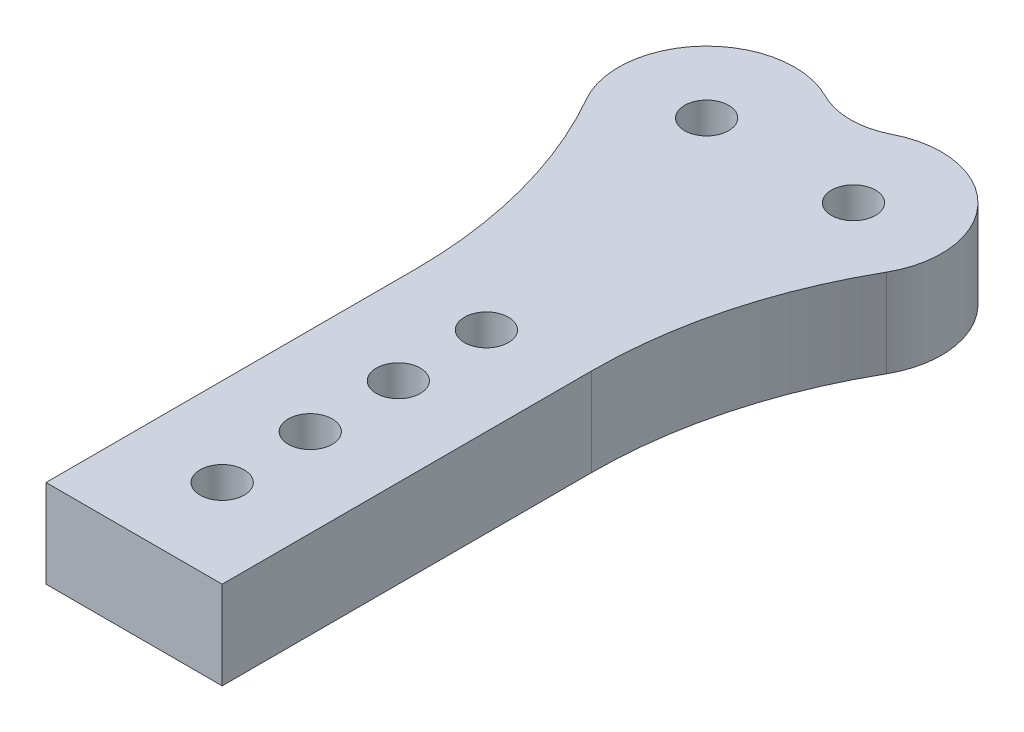
SolidWorks part; units mm, degrees
ref_plane "Alzado" through (0, 0, 0) normal (0, 0, 1) x (1, 0, 0)
ref_plane "Planta" through (0, 0, 0) normal (0, 1, 0) x (1, 0, 0)
ref_plane "Vista lateral" through (0, 0, 0) normal (1, 0, 0) x (0, 0, -1)
sketch "Croquis2" plane through (0, 0, 0) normal (0, 1, 0) x (1, 0, 0)
  line L5 (-14.213, -7.8357) -> (-14.2804, -16.8354) construction
  line L6 (-16.9314, -1.1122) -> (-10.9314, -1.1122) construction
  line L9 (-16.9314, -23.1122) -> (-10.9314, -23.1122)
  line L11 (-16.9314, -1.1122) -> (-10.9314, -1.1122)
  line L13 (-16.9314, -1.1122) -> (-16.9314, -23.1122)
  line L14 (-10.9314, -1.1122) -> (-10.9314, -23.1122)
  circle A1 centre (-13.9314, -20.1122) radius 0.75 construction
  dimension "D1" = 6
  dimension "D2" = 3
  dimension "D3" = 22
extrude "Saliente-Extruir2" add sketch "Croquis2" along normal blind 3
sketch "Croquis7" plane through (0, 3, 0) normal (0, 1, 0) x (1, 0, 0)
  line L0 (-13.9314, -1.1122) -> (-16.4314, -1.1122) construction
  line L1 (-10.9314, -1.1122) -> (-16.9314, -1.1122) construction
  line L2 (-13.9314, -1.1122) -> (-11.4314, -1.1122) construction
  circle A4 centre (-16.4314, -1.1122) radius 3
  circle A6 centre (-11.4314, -1.1122) radius 3
  dimension "D1" = 2.5
  dimension "D3" = 6
  dimension "D4" = 6
  dimension "D2" = 2.5
extrude "Saliente-Extruir4" add sketch "Croquis7" against normal blind 3
fillet "Redondeo2" radius 2.5 1 edges at (-13.9314, 1.5, -0.5461)
sketch "Croquis11" plane through (0, 3, 0) normal (0, 1, 0) x (1, 0, 0)
  line L0 (-19.4314, -1.1122) -> (-8.4314, -1.1122) construction
  line L1 (-13.9314, -23.1122) -> (-13.9314, -1.1122) construction
  line L2 (-16.9314, -23.1122) -> (-10.9314, -23.1122) construction
  line L3 (-19.4314, -1.1122) -> (-16.4314, -1.1122) construction
  arc A0 (-15.0678, 1.56) -> (-16.9314, -4.0703) centre (-16.4314, -1.1122) ccw construction
  arc A1 (-10.9314, -4.0703) -> (-12.7951, 1.56) centre (-11.4314, -1.1122) ccw construction
  circle A2 centre (-16.4314, -1.1122) radius 0.75
  circle A3 centre (-11.4314, -1.1122) radius 0.75
  dimension "D1" = 1.5
extrude "Cortar-Extruir6" cut sketch "Croquis11" against normal blind 3
sketch "Croquis12" plane through (0, 0, 0) normal (0, -1, 0) x (1, 0, 0)
  line L0 (-13.9314, 23.1122) -> (-13.9314, -1.2868) construction
  line L1 (-16.9314, 23.1122) -> (-10.9314, 23.1122) construction
  arc A0 (-12.7951, -1.56) -> (-15.0678, -1.56) centre (-13.9314, -3.7868) ccw construction
  circle A1 centre (-13.9314, 20.1122) radius 0.75
  circle A3 centre (-13.9314, 17.1122) radius 0.75
  circle A4 centre (-13.9314, 14.1122) radius 0.75
  circle A5 centre (-13.9314, 11.1122) radius 0.75
  point P9 (-13.9314, 20.8196)
  point P12 (-13.9314, 17.1122)
  point P15 (-13.9314, 14.1062)
  point P18 (-13.9314, 11.9876)
  dimension "D1" = 1.5
  dimension "D2" = 1.5
  dimension "D4" = 1.5
  dimension "D7" = 1.5
  dimension "D3" = 3
  dimension "D5" = 3
  dimension "D6" = 3
extrude "Cortar-Extruir7" cut sketch "Croquis12" against normal blind 10
fillet "Redondeo3" radius 16 2 edges at (-16.9314, 1.5, 4.0703) (-10.9314, 1.5, 4.0703)
